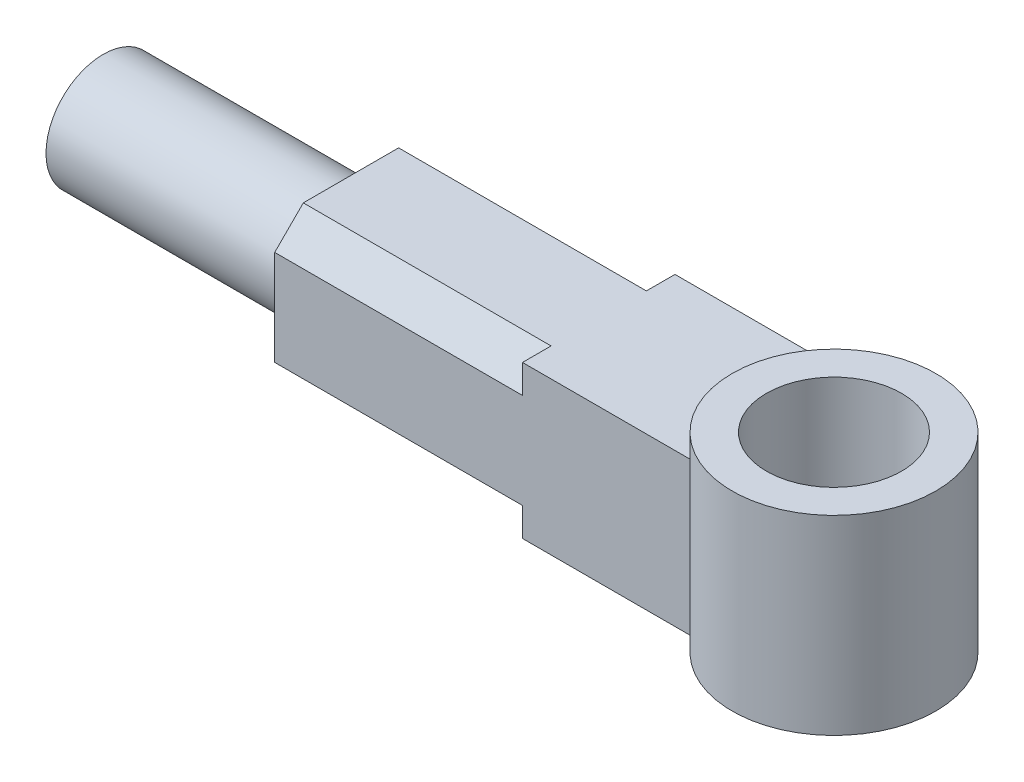
SolidWorks part; units mm, degrees
ref_plane "Front Plane" through (0, 0, 0) normal (0, 0, 1) x (1, 0, 0)
ref_plane "Top Plane" through (0, 0, 0) normal (0, 1, 0) x (1, 0, 0)
ref_plane "Right Plane" through (0, 0, 0) normal (1, 0, 0) x (0, 0, -1)
sketch "Sketch1" plane through (0, 0, 0) normal (0, 0, 1) x (1, 0, 0)
  line L0 (0, 25) -> (9, 25)
  line L1 (9, 25) -> (9, 45)
  line L2 (9, 45) -> (0, 45)
  line L3 (0, -45) -> (9, -45)
  line L4 (9, -45) -> (9, -25)
  line L5 (9, -25) -> (0, -25)
  line L6 (-140.3113, 0) -> (0, 0) construction
  line L7 (-40.3113, 20) -> (-140.3113, 20)
  line L9 (-40.3113, -20) -> (-140.3113, -20)
  line L10 (-140.3113, 20) -> (-140.3113, -20)
  arc A0 (0, 25) -> (0, -25) centre (0, 0) ccw
  arc A1 (0, 45) -> (0, -45) centre (0, 0) ccw
  dimension "D1" = 25
  dimension "D2" = 20
  dimension "D3" = 9
  dimension "D4" = 40
  dimension "D5" = 100
extrude "Boss-Extrude1" add sketch "Sketch1" along normal mid plane 40 contours L10 L6 A1 L7 | L6 L10 L9 A1 | A1 L6 A0 L0 L1 L2 | L6 A1 L3 L4 L5 A0
sketch "Sketch2" plane through (0, 45, 0) normal (0, 1, 0) x (1, 0, 0)
  line L0 (9, -20) -> (9, 20) construction
  circle A0 centre (26.7222, 0) radius 26.7222
  circle A1 centre (26.7222, 0) radius 17.7222
extrude "Boss-Extrude2" add sketch "Sketch2" against normal blind 20
mirror "Mirror1" about plane through (0, 0, 0) normal (0, 1, 0) of "Boss-Extrude2"
sketch "Sketch3" plane through (-140.3113, 0, 0) normal (-1, 0, 0) x (0, 0, 1)
  line L0 (20, 20) -> (-20, 20) construction
  line L1 (-20, 20) -> (-20, -20) construction
  line L4 (-12.5, 20) -> (-20, 20)
  line L5 (-20, 20) -> (-20, 12.5)
  line L8 (-12.5, 20) -> (-20, 12.5)
  dimension "D1" = 45
  dimension "D2" = 7.5
extrude "Cut-Extrude1" cut sketch "Sketch3" against normal blind 65
sketch "Sketch4" plane through (-140.3113, 0, 0) normal (-1, 0, 0) x (0, 0, 1)
  circle A0 centre (0, 0) radius 15
  dimension "D1" = 30
extrude "Boss-Extrude3" add sketch "Sketch4" along normal blind 65
pattern_circular "CirPattern1" count 4 over 360 about axis through (0, 0, 0) along (1, 0, 0) of "Cut-Extrude1"
sketch "Sketch5" plane through (0, 0, 20) normal (0, 0, 1) x (1, 0, 0)
  line L0 (-40.3113, 0) -> (58.4444, 0) construction
  line L1 (-40.3113, 50) -> (58.4444, 50)
  line L2 (-40.3113, 50) -> (-40.3113, -50)
  line L3 (-40.3113, -50) -> (58.4444, -50)
  line L4 (58.4444, 50) -> (58.4444, -50)
  line L5 (53.4444, 45) -> (9, 45) construction
  line L6 (53.4444, 25) -> (53.4444, 45) construction
  dimension "D1" = 5
  dimension "D2" = 5
extrude "Cut-Extrude2" cut sketch "Sketch5" against normal through all both and the other way through all
other "Move Face1" face at (-40.3113, 0, 0) parameters "D1"=9
sketch "Sketch6" plane through (0, 20, 0) normal (0, 1, 0) x (1, 0, 0)
  line L0 (-40.3113, 20) -> (-40.3113, -20) construction
  line L1 (-31.3113, 20) -> (-75.3113, 20) construction
  line L2 (-31.3113, -20) -> (-75.3113, -20) construction
  line L3 (-31.3113, -20) -> (-31.3113, 20) construction
  circle A0 centre (-13.5891, 0) radius 26.7222
  circle A1 centre (-13.5891, 0) radius 17.7222
  dimension "D1" = 9
extrude "Boss-Extrude4" add sketch "Sketch6" along normal blind 5 and the other way blind 45
